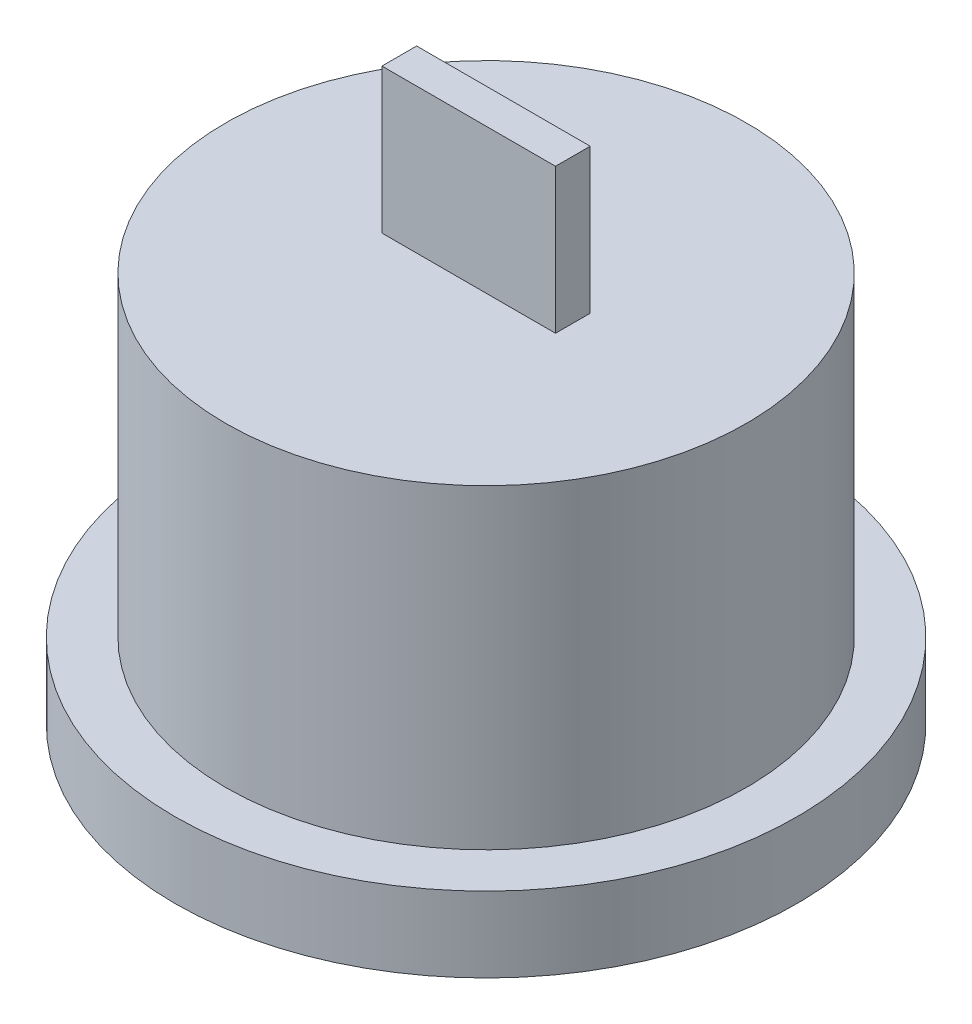
SolidWorks part; units mm, degrees
ref_plane "Front Plane" through (0, 0, 0) normal (0, 0, 1) x (1, 0, 0)
ref_plane "Top Plane" through (0, 0, 0) normal (0, 1, 0) x (1, 0, 0)
ref_plane "Right Plane" through (0, 0, 0) normal (1, 0, 0) x (0, 0, -1)
sketch "Sketch1" plane through (0, 0, 0) normal (0, 1, 0) x (1, 0, 0)
  circle A0 centre (0, 0) radius 10.75
  dimension "D1" = 21.5
extrude "Boss-Extrude1" add sketch "Sketch1" along normal blind 2.6
sketch "Sketch2" plane through (0, 2.6, 0) normal (0, 1, 0) x (1, 0, 0)
  circle A0 centre (0, 0) radius 9
  dimension "D1" = 18
extrude "Boss-Extrude2" add sketch "Sketch2" along normal offset from surface (10.9 mm away) 13.5 up to face at (0, 0, 10.75)
sketch "Sketch3" plane through (0, 13.5, 0) normal (0, 1, 0) x (1, 0, 0)
  line L1 (-3, 0.6) -> (3, 0.6)
  line L2 (-3, 0.6) -> (-3, -0.6)
  line L3 (-3, -0.6) -> (3, -0.6)
  line L4 (3, 0.6) -> (3, -0.6)
  line L5 (-3, 0.6) -> (3, -0.6) construction
  line L6 (-3, -0.6) -> (3, 0.6) construction
  point P0 (0, 0)
  dimension "D1" = 6
  dimension "D2" = 1.2
extrude "Boss-Extrude3" add sketch "Sketch3" along normal blind 5
sketch "Sketch4" plane through (0, 0, 0) normal (0, -1, 0) x (1, 0, 0)
  circle A0 centre (0, 0) radius 9
  dimension "D1" = 18
extrude "Cut-Extrude2" cut sketch "Sketch4" against normal blind 2
sketch "Sketch5" plane through (0, 2, 0) normal (0, -1, 0) x (1, 0, 0)
  line L0 (-3, -0.2) -> (-2.3, -0.9)
  line L1 (-3, 0.9) -> (3, 0.9)
  line L2 (-3, 0.9) -> (-3, -0.9)
  line L3 (-3, -0.9) -> (3, -0.9)
  line L4 (3, 0.9) -> (3, -0.9)
  line L5 (-3, 0.9) -> (3, -0.9) construction
  line L6 (-3, -0.9) -> (3, 0.9) construction
  line L7 (0, 0.9) -> (0, -0.9) construction
  line L8 (3, -0.2) -> (2.3, -0.9)
  point P0 (0, 0)
  dimension "D1" = 6
  dimension "D2" = 1.8
  dimension "D3" = 45
  dimension "D4" = 0.7
extrude "Cut-Extrude3" cut sketch "Sketch5" against normal blind 5 contours L8 L4 L1 L2 L0 L3
